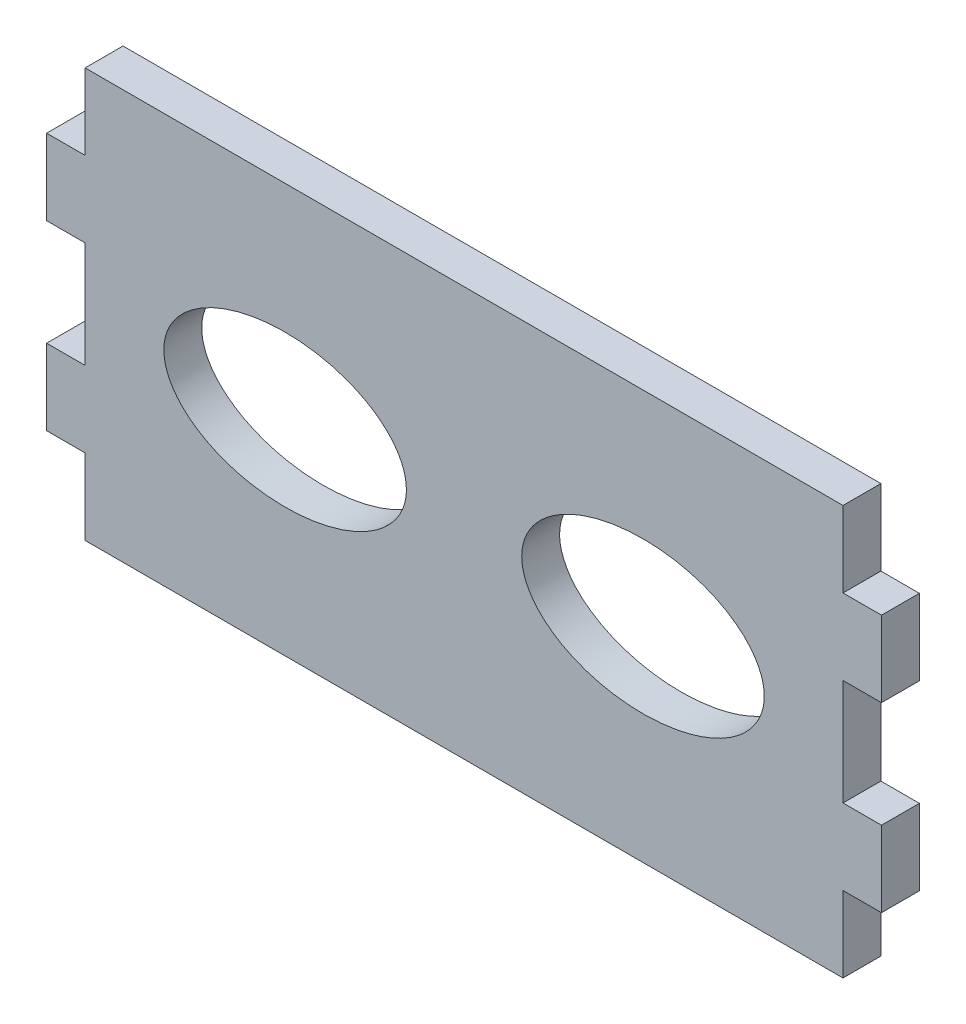
SolidWorks part; units mm, degrees
ref_plane "Front Plane" through (0, 0, 0) normal (0, 0, 1) x (1, 0, 0)
ref_plane "Top Plane" through (0, 0, 0) normal (0, 1, 0) x (1, 0, 0)
ref_plane "Right Plane" through (0, 0, 0) normal (1, 0, 0) x (0, 0, -1)
sketch "Sketch1" plane through (0, 0, 0) normal (0, 0, 1) x (1, 0, 0)
  line L1 (-31.75, -17.145) -> (31.75, -17.145)
  line L2 (-31.75, -17.145) -> (-31.75, 17.145)
  line L3 (-31.75, 17.145) -> (31.75, 17.145)
  line L4 (31.75, -17.145) -> (31.75, 17.145)
  line L5 (-31.75, -17.145) -> (31.75, 17.145) construction
  line L6 (-31.75, 17.145) -> (31.75, -17.145) construction
  point P0 (0, 0)
  dimension "D1" = 63.5
  dimension "D2" = 34.29
extrude "Boss-Extrude1" add sketch "Sketch1" along normal blind 3.175
sketch "Sketch2" plane through (0, 0, 3.175) normal (0, 0, 1) x (1, 0, 0)
  line L0 (-31.75, 10.795) -> (-34.9758, 10.795)
  line L1 (-31.75, 17.145) -> (-31.75, -17.145) construction
  line L2 (-34.9758, 10.795) -> (-34.9758, 4.445)
  line L3 (-34.9758, 4.445) -> (-31.75, 4.445)
  line L4 (-31.75, 4.445) -> (-31.75, 10.795)
  line L5 (-31.75, -4.445) -> (-34.9758, -4.445)
  line L6 (-34.9758, -4.445) -> (-34.9758, -10.795)
  line L7 (-34.9758, -10.795) -> (-31.75, -10.795)
  line L8 (-31.75, -10.795) -> (-31.75, -4.445)
  line L9 (31.75, 17.145) -> (-31.75, 17.145) construction
  dimension "D1" = 3.2258
  dimension "D2" = 6.35
  dimension "D3" = 6.35
  dimension "D4" = 3.2258
  dimension "D5" = 6.35
  dimension "D6" = 8.89
extrude "Boss-Extrude2" add sketch "Sketch2" against normal blind 3.175
mirror "Mirror1" about plane through (0, 0, 0) normal (1, 0, 0) of "Boss-Extrude2"
sketch "Sketch3" plane through (0, 0, 0) normal (0, 0, -1) x (-1, 0, 0)
  ellipse E0 centre (-14.9922, 0) end of major axis (-25.1522, 0) minor radius 6.35
  dimension "D1" = 6.35
  dimension "D2" = 10.16
extrude "cut for lip motor cables" cut sketch "Sketch3" against normal through all
mirror "Mirror2" about plane through (0, 0, 0) normal (1, 0, 0) of "cut for lip motor cables"
